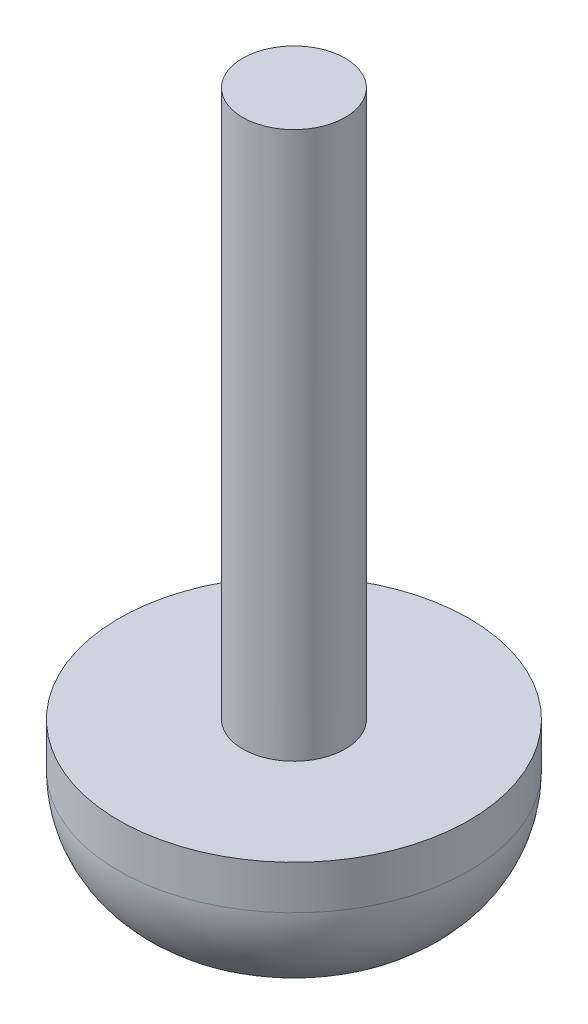
SolidWorks part; units mm, degrees
material "AISI 316 Annealed Stainless Steel Bar (SS)"
ref_plane "Front Plane" through (0, 0, 0) normal (0, 0, 1) x (1, 0, 0)
ref_plane "Top Plane" through (0, 0, 0) normal (0, 1, 0) x (1, 0, 0)
ref_plane "Right Plane" through (0, 0, 0) normal (1, 0, 0) x (0, 0, -1)
sketch "Sketch1" plane through (0, 0, 0) normal (0, 1, 0) x (1, 0, 0)
  circle A0 centre (0, 0) radius 0.5953
  dimension "D1" = 1.1906
extrude "Boss-Extrude1" add sketch "Sketch1" along normal mid plane 6.35
sketch "Sketch2" plane through (0, -3.175, 0) normal (0, -1, 0) x (1, 0, 0)
  circle A0 centre (0, 0) radius 2.032
  dimension "D1" = 4.064
extrude "Boss-Extrude2" add sketch "Sketch2" along normal blind 1.778
fillet "Fillet1" radius 1.27 1 edges at (0, -4.953, -2.032)
sketch "Sketch3" plane through (0, -4.953, 0) normal (0, -1, 0) x (1, 0, 0)
  line L0 (-0.508, -0.508) -> (-1.27, -0.508)
  line L1 (1.27, 0.508) -> (0.508, 0.508)
  line L2 (1.27, 0.508) -> (1.27, -0.508)
  line L3 (1.27, -0.508) -> (0.508, -0.508)
  line L4 (-1.27, 0.508) -> (-1.27, -0.508)
  line L5 (1.27, 0.508) -> (-1.27, -0.508) construction
  line L6 (1.27, -0.508) -> (-1.27, 0.508) construction
  line L7 (0.508, 1.27) -> (-0.508, 1.27)
  line L8 (0.508, 1.27) -> (0.508, 0.508)
  line L9 (0.508, -1.27) -> (-0.508, -1.27)
  line L10 (-0.508, 1.27) -> (-0.508, 0.508)
  line L11 (0.508, 1.27) -> (-0.508, -1.27) construction
  line L12 (0.508, -1.27) -> (-0.508, 1.27) construction
  line L13 (-0.508, -0.508) -> (-0.508, -1.27)
  line L14 (-0.508, 0.508) -> (-1.27, 0.508)
  line L15 (0.508, -0.508) -> (0.508, -1.27)
  circle A0 centre (0, 0) radius 2.032 construction
  point P0 (0, 0)
  point P6 (0, 0)
  dimension "D1" = 1.27
  dimension "D2" = 1.016
extrude "Cut-Extrude1" cut sketch "Sketch3" along a picked direction on the side against the normal blind 1.27
